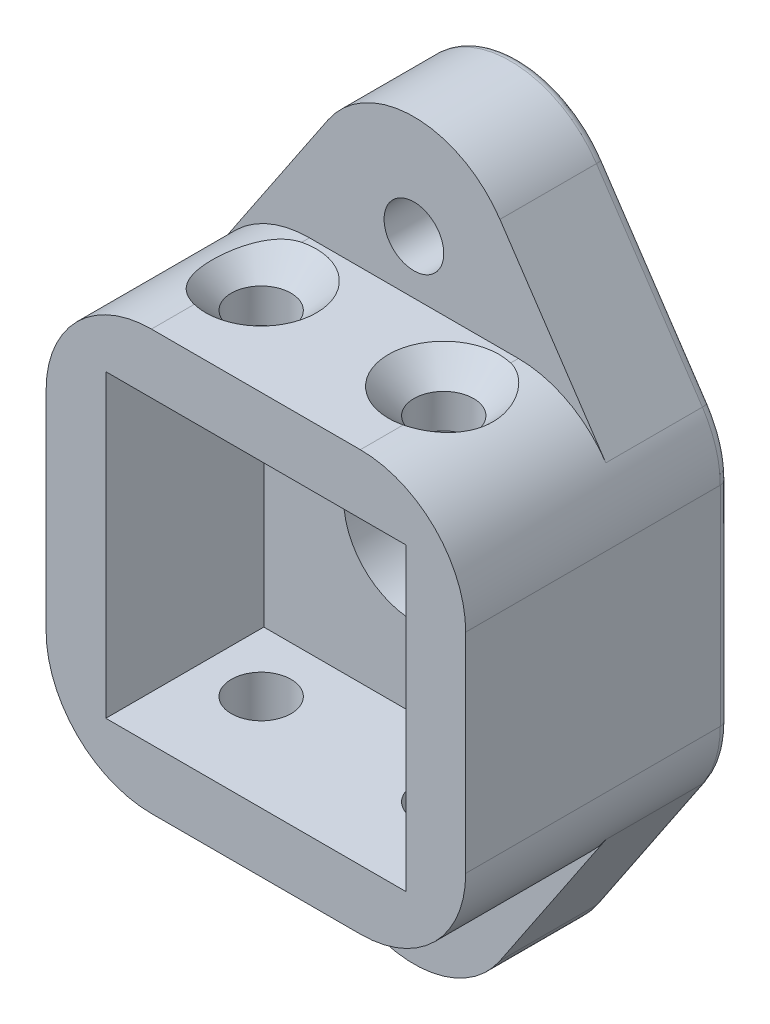
SolidWorks part; units mm, degrees
ref_plane "Plan de face" through (0, 0, 0) normal (0, 0, 1) x (1, 0, 0)
ref_plane "Plan de dessus" through (0, 0, 0) normal (0, 1, 0) x (1, 0, 0)
ref_plane "Plan de droite" through (0, 0, 0) normal (1, 0, 0) x (0, 0, -1)
sketch "Sketch1" plane through (0, 0, 0) normal (0, 0, 1) x (1, 0, 0)
  line L1 (-11.95, -11.95) -> (11.95, -11.95)
  line L2 (-11.95, -11.95) -> (-11.95, 11.95)
  line L3 (-11.95, 11.95) -> (11.95, 11.95)
  line L4 (11.95, -11.95) -> (11.95, 11.95)
  line L5 (-11.95, -11.95) -> (11.95, 11.95) construction
  line L6 (-11.95, 11.95) -> (11.95, -11.95) construction
  line L7 (-8.55, -8.55) -> (8.55, -8.55)
  line L8 (-8.55, -8.55) -> (-8.55, 8.55)
  line L9 (-8.55, 8.55) -> (8.55, 8.55)
  line L10 (8.55, -8.55) -> (8.55, 8.55)
  line L11 (-8.55, -8.55) -> (8.55, 8.55) construction
  line L12 (-8.55, 8.55) -> (8.55, -8.55) construction
  point P0 (0, 0)
  point P5 (0, 0)
  dimension "D1" = 23.9
  dimension "D2" = 23.9
  dimension "D3" = 17.1
  dimension "D4" = 17.1
extrude "Boss-Extrude1" add sketch "Sketch1" along normal blind 15
fillet "Fillet1" radius 6 4 edges at (-11.95, -11.95, 7.5) (11.95, -11.95, 7.5) (11.95, 11.95, 7.5) (-11.95, 11.95, 7.5)
sketch "Sketch3" plane through (0, 0, 0) normal (0, 0, -1) x (-1, 0, 0)
  line L4 (-5.95, -11.95) -> (5.95, -11.95)
  line L5 (11.95, -5.95) -> (11.95, 5.95)
  line L6 (5.95, 11.95) -> (-5.95, 11.95)
  line L7 (-11.95, 5.95) -> (-11.95, -5.95)
  line L8 (-5.95, -11.95) -> (5.95, -11.95)
  line L9 (11.95, -5.95) -> (11.95, 5.95)
  line L10 (5.95, 11.95) -> (-5.95, 11.95)
  line L11 (-11.95, 5.95) -> (-11.95, -5.95)
  circle A0 centre (0, 0) radius 4
  arc A4 (5.95, -11.95) -> (11.95, -5.95) centre (5.95, -5.95) ccw
  arc A5 (11.95, 5.95) -> (5.95, 11.95) centre (5.95, 5.95) ccw
  arc A6 (-5.95, 11.95) -> (-11.95, 5.95) centre (-5.95, 5.95) ccw
  arc A7 (-11.95, -5.95) -> (-5.95, -11.95) centre (-5.95, -5.95) ccw
  arc A8 (5.95, -11.95) -> (11.95, -5.95) centre (5.95, -5.95) ccw
  arc A9 (11.95, 5.95) -> (5.95, 11.95) centre (5.95, 5.95) ccw
  arc A10 (-5.95, 11.95) -> (-11.95, 5.95) centre (-5.95, 5.95) ccw
  arc A11 (-11.95, -5.95) -> (-5.95, -11.95) centre (-5.95, -5.95) ccw
  dimension "D2" = 8
  dimension "D1" = 0
extrude "Boss-Extrude2" add sketch "Sketch3" against normal blind 6
sketch "Sketch2" plane through (0, 0, 0) normal (0, 0, -1) x (-1, 0, 0)
  line L0 (0, 15) -> (0, 11.95) construction
  line L3 (-5.95, 11.95) -> (5.95, 11.95) construction
  line L8 (5.9001, 11.95) -> (-5.9, 11.95)
  line L10 (10.9329, 9.2923) -> (4.8998, 18.2866)
  line L11 (-4.8998, 18.2866) -> (-10.9329, 9.2923)
  line L12 (0, 0) -> (2.476, 0) construction
  line L13 (0, -15) -> (0, -11.95) construction
  line L14 (-4.8998, -18.2866) -> (-10.9329, -9.2923)
  line L16 (10.9329, -9.2923) -> (4.8998, -18.2866)
  line L17 (5.9001, -11.95) -> (-5.9, -11.95)
  arc A0 (4.8998, 18.2866) -> (-4.8998, 18.2866) centre (0, 15) ccw
  arc A4 (11.95, 5.95) -> (5.95, 11.95) centre (5.95, 5.95) ccw construction
  arc A5 (10.9329, 9.2923) -> (5.95, 11.95) centre (5.95, 5.95) ccw
  arc A6 (-5.95, 11.95) -> (-11.95, 5.95) centre (-5.95, 5.95) ccw construction
  arc A7 (-5.95, 11.95) -> (-10.9329, 9.2923) centre (-5.95, 5.95) ccw
  arc A8 (-5.95, -11.95) -> (-10.9329, -9.2923) centre (-5.95, -5.95) cw
  arc A9 (10.9329, -9.2923) -> (5.95, -11.95) centre (5.95, -5.95) cw
  arc A10 (4.8998, -18.2866) -> (-4.8998, -18.2866) centre (0, -15) cw
  dimension "D1" = 5.9
  dimension "D2" = 3.05
extrude "Boss-Extrude3" add sketch "Sketch2" against normal blind 6
hole_wizard "CBORE for M3 Hex Socket Head Cap Screw1" positions "Sketch4" profile "Sketch5" counterbore size "M3" standard "ISO" end condition through all
sketch "Sketch4" plane through (0, 0, 0) normal (0, 0, -1) x (-1, 0, 0)
  point P0 (0, 15)
  point P3 (0, -15)
sketch "Sketch5" plane through (0, 15, 0) normal (1, 0, 0) x (0, 1, 0)
  line L0 (0, 0) -> (0, 15)
  line L1 (0, 15) -> (1.7, 15)
  line L3 (1.7, 15) -> (1.7, 3.4)
  line L4 (1.7, 3.4) -> (3.25, 3.4)
  line L5 (3.25, 3.4) -> (3.25, 0)
  line L7 (3.25, 0) -> (0, 0)
  line L11 (0, -6.35) -> (0, 107.95) construction
  dimension "Thru Hole Dia." = 3.4
  dimension "Thru Hole Depth" = 15
  dimension "C'Bore Dia." = 6.5
  dimension "C'Bore Depth" = 3.4
fillet "Fillet2" radius 0.5 12 edges at (11.6901, 7.6968, 0) (11.95, 0, 0) (-11.6901, 7.6968, 0) (-11.6901, -7.6968, 0) (11.6901, -7.6968, 0) (-11.95, 0, 0) (7.9163, 13.7895, 0) (0, 20.9, 0) (-7.9163, 13.7895, 0) (7.9163, -13.7895, 0) (0, -20.9, 0) (-7.9163, -13.7895, 0)
hole_wizard "CSK for M3 Countersunk Flat Head Screw1" positions "Sketch7" profile "Sketch9" countersink size "M3" standard "ISO" end condition through all
sketch "Sketch7" plane through (0, 11.95, 0) normal (0, 1, 0) x (1, 0, 0)
  line L0 (4.4846, 0) -> (-4.4846, 0) construction
  point P0 (-5.2, -9.5)
  point P2 (5.2, -9.5)
  point P7 (0, 0)
  dimension "D1" = 10.4
  dimension "D2" = 5.2
  dimension "D3" = 9.5
sketch "Sketch9" plane through (-5.2, 11.95, 9.5) normal (1, 0, 0) x (0, 0, 1)
  line L0 (0, 0) -> (0, 32.85)
  line L1 (0, 32.85) -> (1.7, 32.85)
  line L2 (1.7, 32.85) -> (1.7, 1.45)
  line L3 (1.7, 1.45) -> (3.15, 0)
  line L5 (3.15, 0) -> (0, 0)
  line L6 (-1.7, 1.45) -> (-3.15, 0) construction
  line L11 (0, -6.35) -> (0, 107.95) construction
  dimension "Thru Hole Dia." = 3.4
  dimension "Thru Hole Depth" = 32.85
  dimension "Near C'Sink Dia." = 6.3
  dimension "Near C'Sink Angle" = 90
